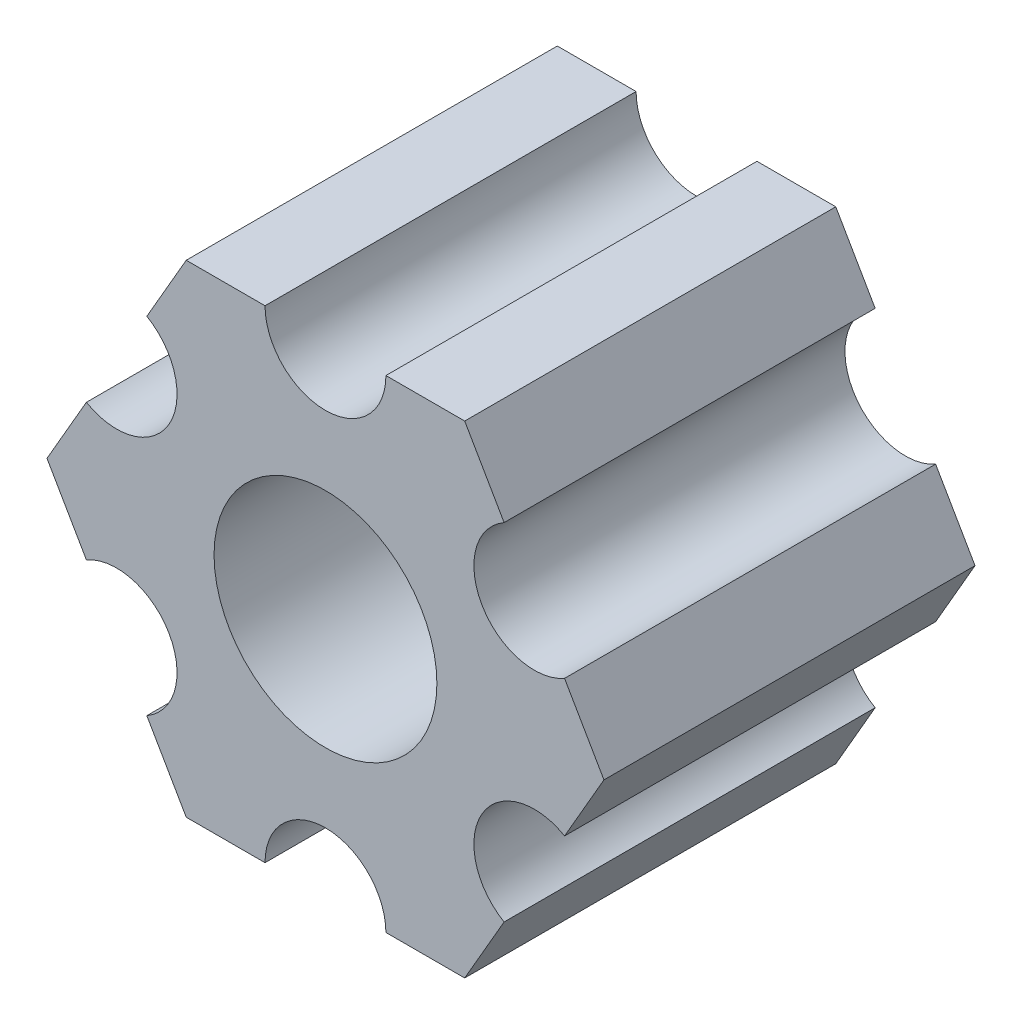
SolidWorks part; units mm, degrees
ref_plane "Front Plane" through (0, 0, 0) normal (0, 0, 1) x (1, 0, 0)
ref_plane "Top Plane" through (0, 0, 0) normal (0, 1, 0) x (1, 0, 0)
ref_plane "Right Plane" through (0, 0, 0) normal (1, 0, 0) x (0, 0, -1)
ref_plane "Plane1" through (0, 0, 0) normal (0, 0, -1) x (-1, 0, 0)
sketch "Sketch1" plane through (0, 0, 0) normal (0, 0, -1) x (-1, 0, 0)
  line L0 (-4.7036, -4.5531) -> (-3.6662, -6.35)
  line L1 (-3.6662, -6.35) -> (-1.5913, -6.35)
  line L2 (1.5913, -6.35) -> (3.6662, -6.35)
  line L3 (3.6662, -6.35) -> (4.7036, -4.5531)
  line L4 (6.2949, -1.7969) -> (7.3323, 0)
  line L5 (7.3323, 0) -> (6.2949, 1.7969)
  line L6 (4.7036, 4.5531) -> (3.6662, 6.35)
  line L7 (3.6662, 6.35) -> (1.5913, 6.35)
  line L8 (-1.5913, 6.35) -> (-3.6662, 6.35)
  line L9 (-3.6662, 6.35) -> (-4.7036, 4.5531)
  line L10 (-6.2949, 1.7969) -> (-7.3323, 0)
  line L11 (-7.3323, 0) -> (-6.2949, -1.7969)
  circle A0 centre (0, 0) radius 2.9337
  arc A1 (-6.2949, -1.7969) -> (-4.7036, -4.5531) centre (-5.4993, -3.175) cw
  arc A2 (-1.5913, -6.35) -> (1.5913, -6.35) centre (0, -6.35) cw
  arc A3 (4.7036, -4.5531) -> (6.2949, -1.7969) centre (5.4993, -3.175) cw
  arc A4 (6.2949, 1.7969) -> (4.7036, 4.5531) centre (5.4993, 3.175) cw
  arc A5 (1.5913, 6.35) -> (-1.5913, 6.35) centre (0, 6.35) cw
  arc A6 (-4.7036, 4.5531) -> (-6.2949, 1.7969) centre (-5.4993, 3.175) cw
extrude "Boss-Extrude1" add sketch "Sketch1" against normal blind 9.77
